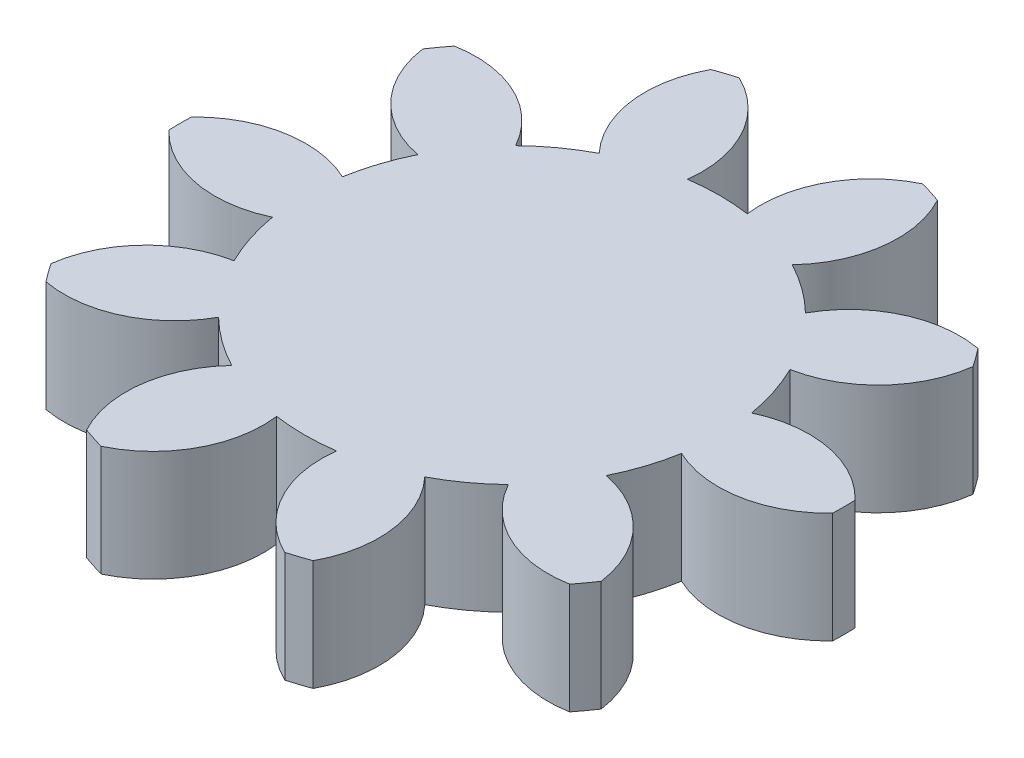
SolidWorks part; units mm, degrees
ref_plane "Front Plane" through (0, 0, 0) normal (0, 0, 1) x (1, 0, 0)
ref_plane "Top Plane" through (0, 0, 0) normal (0, 1, 0) x (1, 0, 0)
ref_plane "Right Plane" through (0, 0, 0) normal (1, 0, 0) x (0, 0, -1)
sketch "Sketch1" plane through (0, 0, 0) normal (0, 1, 0) x (1, 0, 0)
  circle A0 centre (0, 0) radius 9
  dimension "addendumDiameter" = 18
extrude "Boss-Extrude1" add sketch "Sketch1" along normal blind 3
sketch "Sketch2" plane through (0, 3, 0) normal (0, 1, 0) x (1, 0, 0)
  line L0 (0, 0) -> (0, 29.7394) construction
  line L1 (0, 0) -> (-7.1182, 21.9075) construction
  line L2 (-2.2889, 7.0444) -> (-1.1684, 7.4084) construction
  circle A0 centre (0, 0) radius 5.625 construction
  circle A1 centre (0, 0) radius 7.0477 construction
  circle A2 centre (0, 0) radius 7.5 construction
  arc A3 (-2.4893, 8.6489) -> (2.4893, 8.6489) centre (0, 0) cw
  circle A4 centre (0, 0) radius 9 construction
  arc A5 (-2.4893, 8.6489) -> (-0.8106, 5.5663) centre (-3.7867, 5.944) cw
  arc A6 (-0.8106, 5.5663) -> (0.8106, 5.5663) centre (0, 0) cw
  arc A7 (0.8106, 5.5663) -> (2.4893, 8.6489) centre (3.7867, 5.944) cw
  dimension "D1" = 11.25
  dimension "D2" = 14.0954
  dimension "D3" = 15
  dimension "D5" = 3
  dimension "D4" = 18
  dimension "D6" = 1.1781
extrude "Cut-Extrude1" cut sketch "Sketch2" against normal through all
pattern_circular "CirPattern1" count 10 over 360 about axis through (0, 0, 0) along (0, 1, 0) of "Cut-Extrude1"
sketch "Sketch3" plane through (0, 3, 0) normal (0, 1, 0) x (1, 0, 0)
  line L0 (0, 0) -> (0, 15.9419) construction
  line L1 (0, 3) -> (4.7553, 1.4549)
  line L2 (0, 3) -> (-4.7553, 1.4549)
  arc A0 (-4.7553, 1.4549) -> (4.7553, 1.4549) centre (0, 0) cw
  dimension "D1" = 5
  dimension "D2" = 216
  dimension "D3" = 3
extrude "Cut-Extrude2" [suppressed] cut sketch "Sketch3" against normal blind 10
fillet "Fillet1" [suppressed] radius 1
pattern_circular "CirPattern2" [suppressed] count 4 over 360
equation "\"module\"= 1.5"
equation "\"teeth\" = 10"
equation "\"pressureAngle\"= 20"
equation "\"gearThickness\"= 3"
equation "\"addendumFactor\"= 1"
equation "\"dedendumFactor\"= 1.25"
equation "\"pitch\"= 1 / \"module\""
equation "\"pitchDiameter\"= \"teeth\" / \"pitch\""
equation "\"addendum\"= \"addendumFactor\" / \"pitch\""
equation "\"dedendum\"= \"dedendumFactor\" / \"pitch\""
equation "\"addendumDiameter\"=\"pitchDiameter\"+2 *\"addendum\" "
equation "\"addendumDiameter@Sketch1\"=\"pitchDiameter\" + 2 * \"addendum\""
equation "\"D1@Boss-Extrude1\"=\"gearThickness\""
equation "\"D1@Sketch2\"=\"pitchDiameter\" - 2 * \"dedendum\""
equation "\"D2@Sketch2\"=\"pitchDiameter\" * cos ( \"pressureAngle\" )"
equation "\"D3@Sketch2\"=\"pitchDiameter\""
equation "\"D4@Sketch2\"= 180 / \"teeth\""
equation "\"D5@Sketch2\"=\"pitchDiameter\" / 5"
equation "\"D6@Sketch2\"=pi/2 / \"pitch\"/2"
equation "\"D1@CirPattern1\"=\"teeth\""
equation "\"D1@Sketch3\"= \"pitchDiameter\" / 3"
equation "\"D2@Sketch3\"= 360 / ( \"teeth\" / 6 )"
